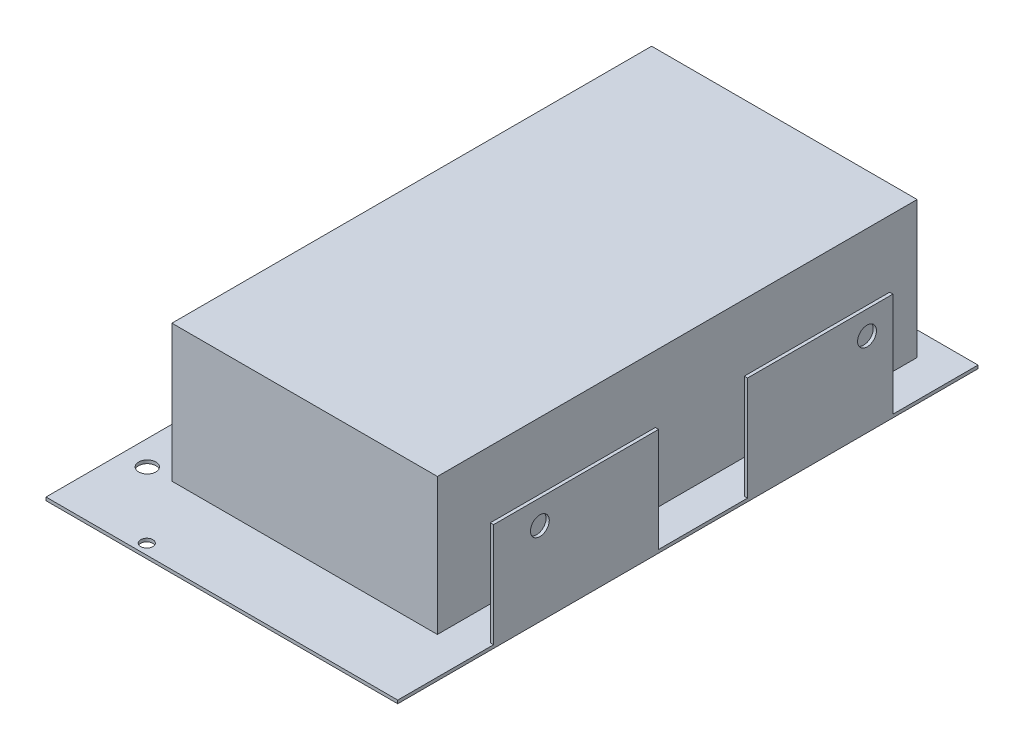
SolidWorks part; units mm, degrees
ref_plane "Front Plane" through (0, 0, 0) normal (0, 0, 1) x (1, 0, 0)
ref_plane "Top Plane" through (0, 0, 0) normal (0, 1, 0) x (1, 0, 0)
ref_plane "Right Plane" through (0, 0, 0) normal (1, 0, 0) x (0, 0, -1)
sketch "Sketch1" plane through (0, 0, 0) normal (0, 1, 0) x (1, 0, 0)
  line L1 (-64.25, 106) -> (64.25, 106)
  line L2 (-64.25, 106) -> (-64.25, -106)
  line L3 (-64.25, -106) -> (64.25, -106)
  line L4 (64.25, 106) -> (64.25, -106)
  line L5 (-64.25, 106) -> (64.25, -106) construction
  line L6 (-64.25, -106) -> (64.25, 106) construction
  circle A0 centre (-55.25, -78) radius 3.15
  circle A1 centre (-31.25, -102.185) radius 2.215
  point P0 (0, 0)
  dimension "D3" = 6.3
  dimension "D7" = 4.43
  dimension "D1" = 128.5
  dimension "D2" = 212
  dimension "D4" = 9
  dimension "D5" = 28
  dimension "D6" = 3.815
  dimension "D8" = 33
extrude "Base" add sketch "Sketch1" along normal blind 1.18
sketch "Sketch4" plane through (0, 1.18, 0) normal (0, 1, 0) x (1, 0, 0)
  line L1 (-46.25, 97.26) -> (50.75, 97.26)
  line L2 (-46.25, 97.26) -> (-46.25, -78)
  line L3 (-46.25, -78) -> (50.75, -78)
  line L4 (50.75, 97.26) -> (50.75, -78)
  point P6 (-55.25, -78)
  dimension "D1" = 9
  dimension "D2" = 97
  dimension "D3" = 175.26
extrude "Capacitors" add sketch "Sketch4" along normal blind 50
sketch "Sketch2" plane through (0, 1.18, 0) normal (0, 1, 0) x (1, 0, 0)
  line L0 (64.25, -106) -> (64.25, 106) construction
  line L1 (64.25, -10.7) -> (63.07, -10.7)
  line L2 (64.25, -10.7) -> (64.25, -71)
  line L3 (64.25, -71) -> (63.07, -71)
  line L4 (63.07, -10.7) -> (63.07, -71)
  line L5 (-64.25, -106) -> (64.25, -106) construction
  line L6 (64.25, 74.9) -> (63.07, 74.9)
  line L7 (64.25, 74.9) -> (64.25, 21.8)
  line L8 (64.25, 21.8) -> (63.07, 21.8)
  line L9 (63.07, 74.9) -> (63.07, 21.8)
  dimension "D1" = 1.18
  dimension "D2" = 35
  dimension "D3" = 60.3
  dimension "D4" = 32.5
  dimension "D5" = 53.1
extrude "Tabs" add sketch "Sketch2" along normal blind 38
sketch "Sketch3" plane through (64.25, 0, 0) normal (1, 0, 0) x (0, 0, -1)
  line L0 (-71, 39.18) -> (-71, 1.18) construction
  line L1 (-71, 39.18) -> (-10.7, 39.18) construction
  line L2 (21.8, 39.18) -> (74.9, 39.18) construction
  line L3 (74.9, 39.18) -> (74.9, 1.18) construction
  circle A0 centre (-54.07, 30.38) radius 3.44
  circle A1 centre (65.46, 30.64) radius 3.45
  dimension "D3" = 6.88
  dimension "D4" = 8.54
  dimension "D6" = 6.9
  dimension "D1" = 16.93
  dimension "D2" = 8.8
  dimension "D5" = 9.44
extrude "Tab Holes" cut sketch "Sketch3" against normal up to next
